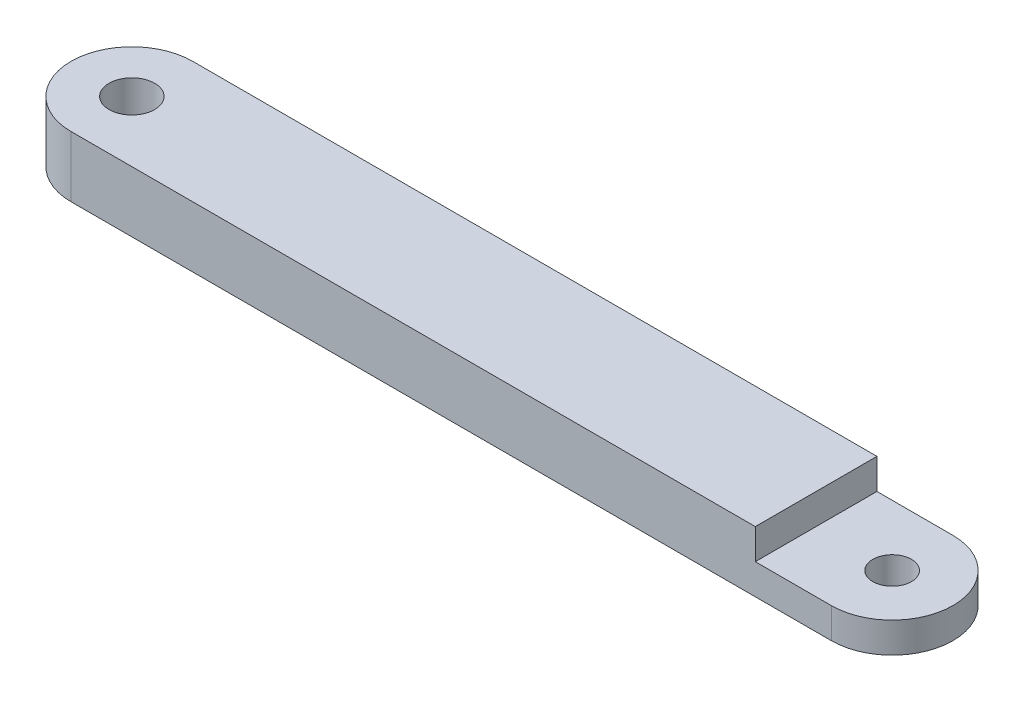
SolidWorks part; units mm, degrees
ref_plane "Front" through (0, 0, 0) normal (0, 0, 1) x (1, 0, 0)
ref_plane "Top" through (0, 0, 0) normal (0, 1, 0) x (1, 0, 0)
ref_plane "Right" through (0, 0, 0) normal (1, 0, 0) x (0, 0, -1)
sketch "Sketch1" plane through (0, 0, 0) normal (0, 1, 0) x (1, 0, 0)
  line L0 (-39.6875, 0) -> (39.6875, 0) construction
  line L1 (-39.6875, 6.35) -> (39.6875, 6.35)
  line L2 (-39.6875, -6.35) -> (39.6875, -6.35)
  arc A0 (-39.6875, 6.35) -> (-39.6875, -6.35) centre (-39.6875, 0) ccw
  arc A1 (39.6875, -6.35) -> (39.6875, 6.35) centre (39.6875, 0) ccw
  point P2 (0, 0)
  dimension "D1" = 79.375
  dimension "D2" = 12.7
extrude "Boss-Extrude1" add sketch "Sketch1" along normal blind 6.35
hole_wizard "3/16 (0.1875) Diameter Hole1" positions "Sketch2" profile "Sketch3" hole size "3/16" standard "ANSI Inch" end condition through all
sketch "Sketch2" plane through (0, 6.35, 0) normal (0, 1, 0) x (1, 0, 0)
  point P0 (-39.6875, 0)
  point P10 (0, 0)
sketch "Sketch3" plane through (-39.6875, 6.35, 0) normal (1, 0, 0) x (0, 0, 1)
  line L0 (0, 0) -> (0, 6.35)
  line L1 (0, 6.35) -> (2.3812, 6.35)
  line L2 (2.3812, 6.35) -> (2.3812, 0)
  line L5 (2.3812, 0) -> (0, 0)
  line L11 (0, -6.35) -> (0, 107.95) construction
  dimension "Thru Hole Dia." = 4.7625
  dimension "Thru Hole Depth" = 6.35
hole_wizard "#21 (0.159) Diameter Hole1" positions "Sketch5" profile "Sketch6" hole size "#21" standard "ANSI Inch" end condition through all
sketch "Sketch5" plane through (0, 6.35, 0) normal (0, 1, 0) x (1, 0, 0)
  point P0 (39.6875, 0)
sketch "Sketch6" plane through (39.6875, 6.35, 0) normal (1, 0, 0) x (0, 0, 1)
  line L0 (0, 0) -> (0, 6.35)
  line L1 (0, 6.35) -> (2.0193, 6.35)
  line L2 (2.0193, 6.35) -> (2.0193, 0)
  line L5 (2.0193, 0) -> (0, 0)
  line L11 (0, -6.35) -> (0, 107.95) construction
  dimension "Thru Hole Dia." = 4.0386
  dimension "Thru Hole Depth" = 6.35
sketch "Sketch4" plane through (0, 6.35, 0) normal (0, 1, 0) x (1, 0, 0)
  line L0 (39.6875, 6.35) -> (-39.6875, 6.35) construction
  line L1 (47.625, -6.35) -> (31.75, -6.35)
  line L2 (47.625, -6.35) -> (47.625, 6.35)
  line L3 (47.625, 6.35) -> (31.75, 6.35)
  line L4 (31.75, -6.35) -> (31.75, 6.35)
  line L5 (47.625, -6.35) -> (31.75, 6.35) construction
  line L6 (47.625, 6.35) -> (31.75, -6.35) construction
  point P0 (39.6875, 0)
  point P8 (0, 0)
  point P9 (39.6875, 0)
  dimension "D1" = 7.9375
extrude "Cut-Extrude1" cut sketch "Sketch4" against normal blind 3.175
